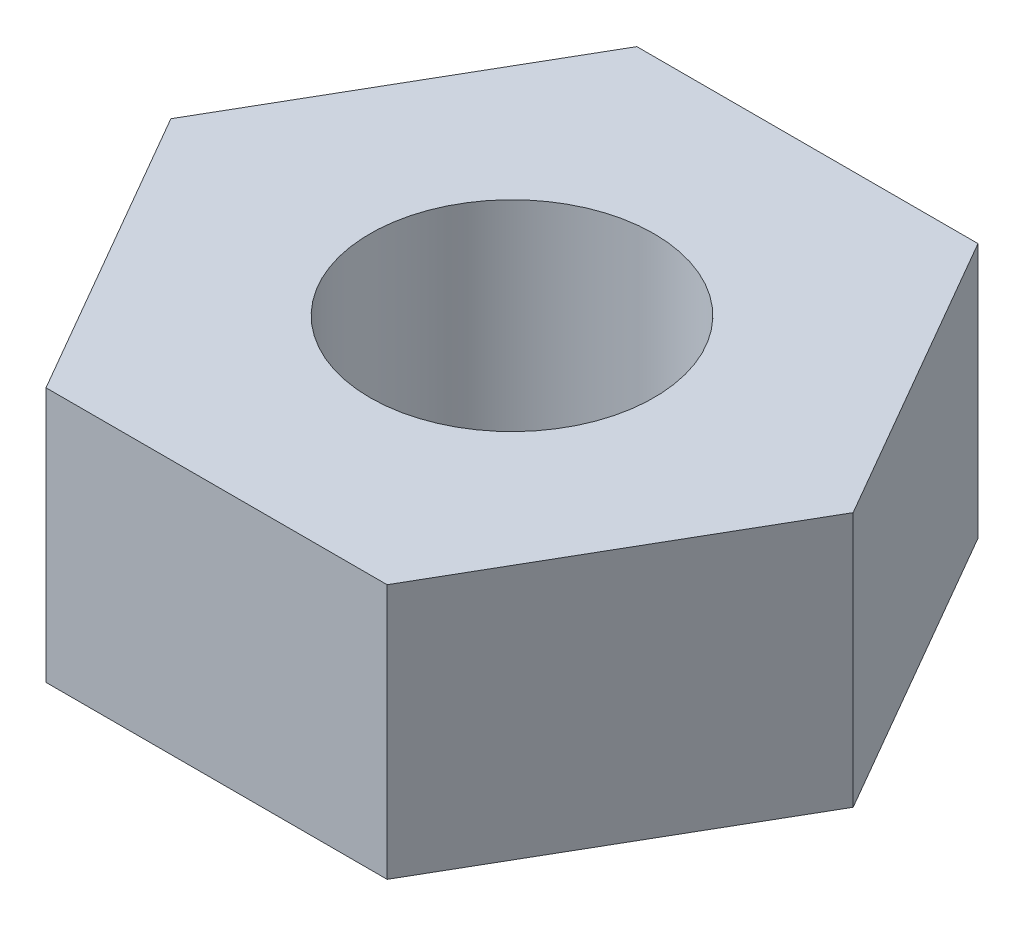
SolidWorks part; units mm, degrees
ref_plane "Front Plane" through (0, 0, 0) normal (0, 0, 1) x (1, 0, 0)
ref_plane "Top Plane" through (0, 0, 0) normal (0, 1, 0) x (1, 0, 0)
ref_plane "Right Plane" through (0, 0, 0) normal (1, 0, 0) x (0, 0, -1)
sketch "Sketch1" plane through (0, 0, 0) normal (0, 1, 0) x (1, 0, 0)
  line L1 (1.1229, -1.945) -> (2.2459, 0)
  line L2 (2.2459, 0) -> (1.1229, 1.945)
  line L3 (1.1229, 1.945) -> (-1.1229, 1.945)
  line L4 (-1.1229, 1.945) -> (-2.2459, 0)
  line L5 (-2.2459, 0) -> (-1.1229, -1.945)
  line L6 (-1.1229, -1.945) -> (1.1229, -1.945)
  circle A0 centre (0, 0) radius 1.945 construction
  dimension "D1" = 3.89
extrude "Boss-Extrude1" add sketch "Sketch1" along normal blind 1.68
sketch "Sketch2" plane through (0, 1.68, 0) normal (0, 1, 0) x (1, 0, 0)
  circle A0 centre (0, 0) radius 0.935
  dimension "D1" = 1.87
extrude "Cut-Extrude1" cut sketch "Sketch2" against normal through all
